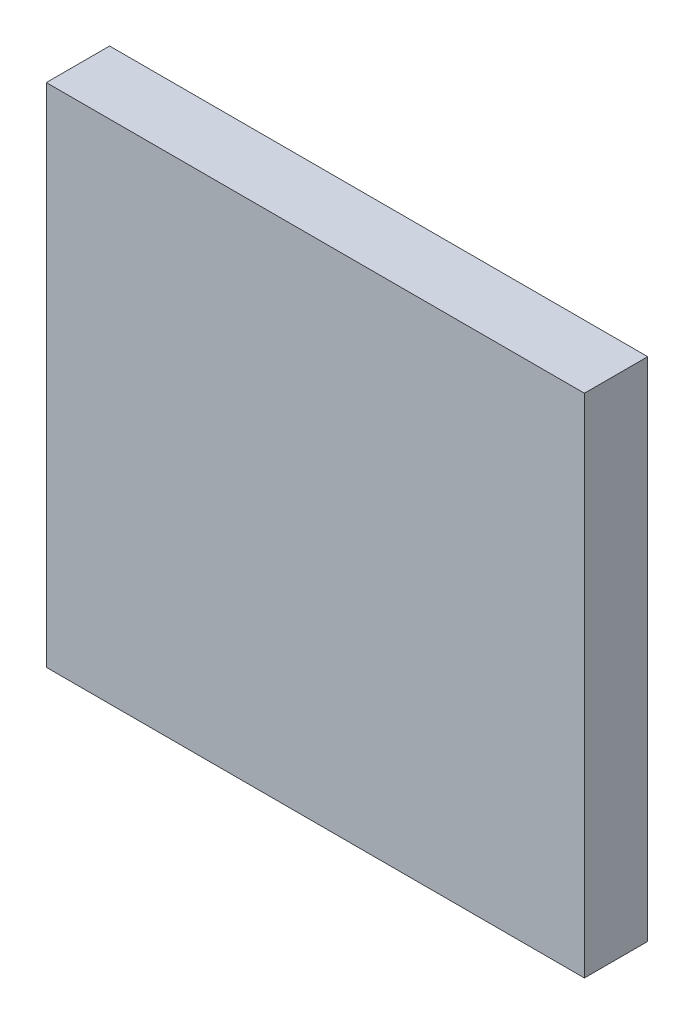
SolidWorks part; units mm, degrees
ref_plane "Front Plane" through (0, 0, 0) normal (0, 0, 1) x (1, 0, 0)
ref_plane "Top Plane" through (0, 0, 0) normal (0, 1, 0) x (1, 0, 0)
ref_plane "Right Plane" through (0, 0, 0) normal (1, 0, 0) x (0, 0, -1)
sketch "Sketch1" plane through (0, 0, 0) normal (0, 0, 1) x (1, 0, 0)
  line L1 (0, -400.8) -> (431.8, -400.8)
  line L2 (0, -400.8) -> (0, 5.6)
  line L3 (0, 5.6) -> (431.8, 5.6)
  line L4 (431.8, -400.8) -> (431.8, 5.6)
  line L7 (0, -400.8) -> (500, -400.8) construction
  dimension "D1" = 406.4
  dimension "D2" = 0
  dimension "D3" = 431.8
extrude "Boss-Extrude1" add sketch "Sketch1" against normal blind 50.8
